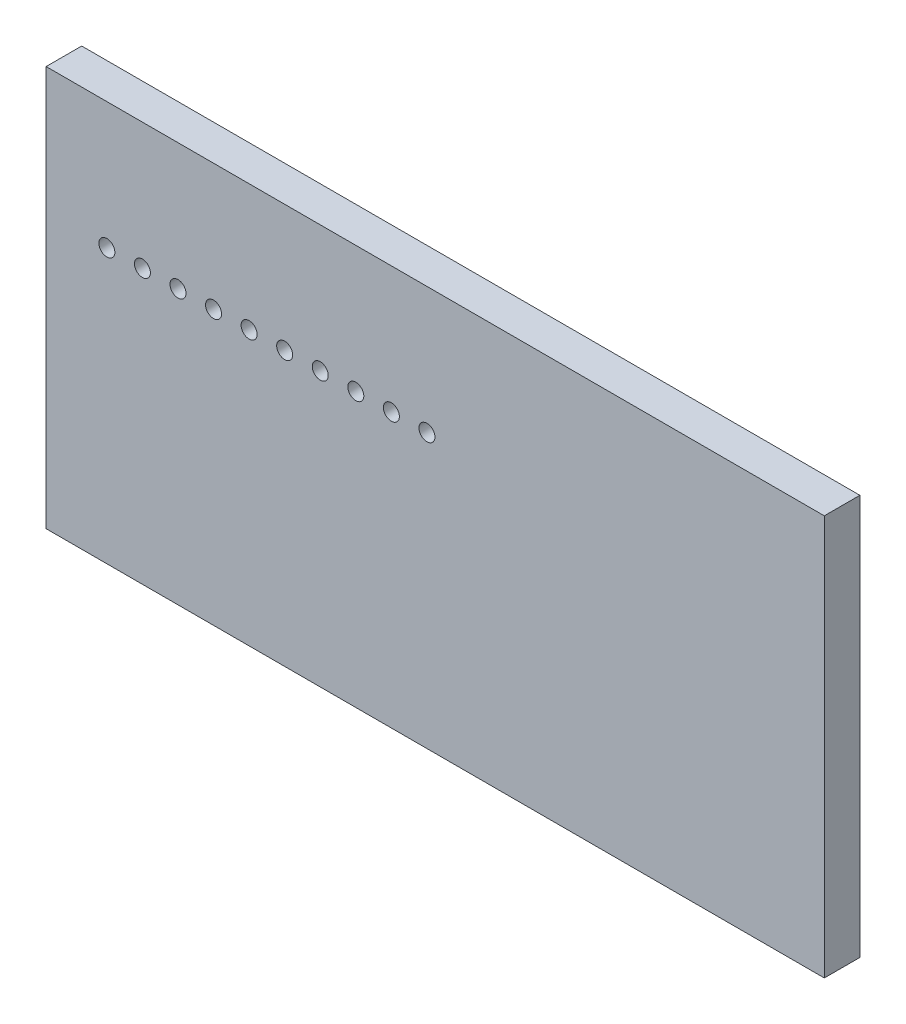
SolidWorks part; units mm, degrees
ref_plane "XY" through (0, 0, 0) normal (0, 0, 1) x (1, 0, 0)
ref_plane "XZ" through (0, 0, 0) normal (0, 1, 0) x (1, 0, 0)
ref_plane "YZ" through (0, 0, 0) normal (1, 0, 0) x (0, 0, -1)
sketch "Esquisse1" plane through (0, 0, 0) normal (0, 0, 1) x (1, 0, 0)
  line L1 (-109.4122, 56.2783) -> (109.4122, 56.2783)
  line L2 (-109.4122, 56.2783) -> (-109.4122, -56.2783)
  line L3 (-109.4122, -56.2783) -> (109.4122, -56.2783)
  line L4 (109.4122, 56.2783) -> (109.4122, -56.2783)
  line L5 (-109.4122, 56.2783) -> (109.4122, -56.2783) construction
  line L6 (-109.4122, -56.2783) -> (109.4122, 56.2783) construction
  point P0 (0, 0)
extrude "Boss.-Extru.1" add sketch "Esquisse1" along normal blind 10
hole_wizard "Dégagement M41" positions "Esquisse2" profile "Esquisse3" hole size "M4" standard "ISO" end condition up to next
sketch "Esquisse2" plane through (0, 0, 10) normal (0, 0, 1) x (1, 0, 0)
  point P0 (-92.3323, 20.6904)
sketch "Esquisse3" plane through (-92.3323, 20.6904, 10) normal (1, 0, 0) x (0, -1, 0)
  line L0 (0, 0) -> (0, 10)
  line L1 (0, 10) -> (2.25, 10)
  line L2 (2.25, 10) -> (2.25, 0)
  line L5 (2.25, 0) -> (0, 0)
  line L11 (0, -6.35) -> (0, 107.95) construction
  dimension "Diamètre du perçage jusqu'au prochain" = 4.5
  dimension "Profondeur du perçage jusqu'au prochain" = 10
pattern_linear "Répétition linéaire1" count 10 spacing 10 along (1, 0, 0) of "Dégagement M41"
equation "\"NB01\"= 10"
equation "\"D1@Répétition linéaire1\" = \"NB01\""
equation "\"NB02\"= 8"
